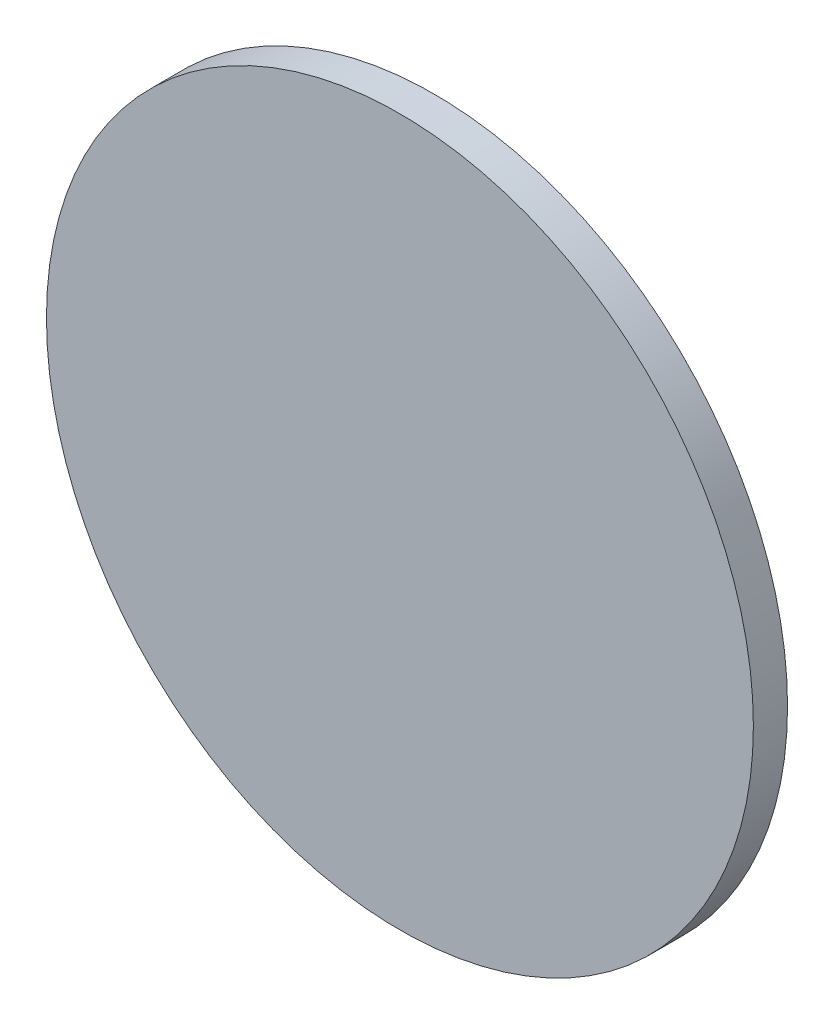
SolidWorks part; units mm, degrees
material "ABS PC"
ref_plane "Front Plane" through (0, 0, 0) normal (0, 0, 1) x (1, 0, 0)
ref_plane "Top Plane" through (0, 0, 0) normal (0, 1, 0) x (1, 0, 0)
ref_plane "Right Plane" through (0, 0, 0) normal (1, 0, 0) x (0, 0, -1)
sketch "Sketch1" plane through (0, 0, 0) normal (0, 0, 1) x (1, 0, 0)
  circle A0 centre (0, 0) radius 16.4211
  dimension "D1" = 32.8422
extrude "Boss-Extrude1" add sketch "Sketch1" along normal blind 1.5875
